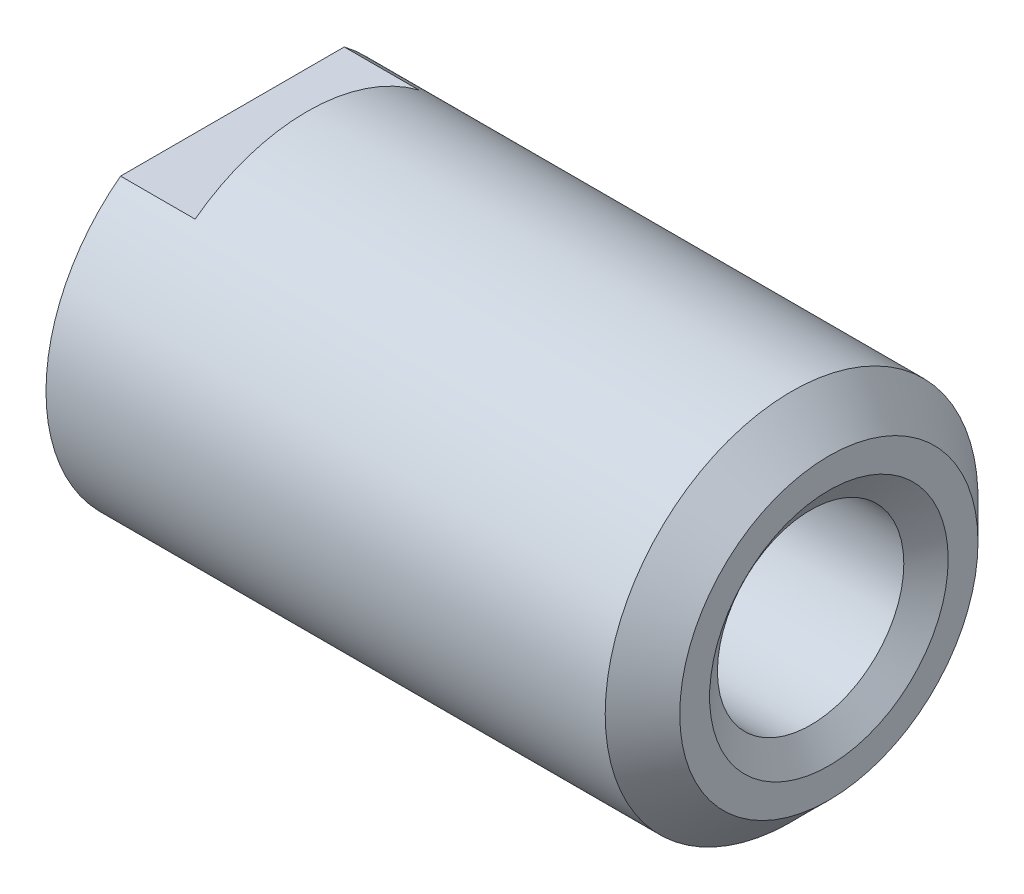
SolidWorks part; units mm, degrees
ref_plane "Спереди" through (0, 0, 0) normal (0, 0, 1) x (1, 0, 0)
ref_plane "Сверху" through (0, 0, 0) normal (0, 1, 0) x (1, 0, 0)
ref_plane "Справа" through (0, 0, 0) normal (1, 0, 0) x (0, 0, -1)
sketch "Эскиз1" plane through (0, 0, 0) normal (0, 0, 1) x (1, 0, 0)
  line L0 (0, 0) -> (16.4018, 0) construction
  line L1 (0, 1.25) -> (0, 2.5)
  line L2 (0, 2.5) -> (8, 2.5)
  line L3 (8, 2.5) -> (8, 1.25)
  line L4 (8, 1.25) -> (0, 1.25)
  dimension "D1" = 2.5
  dimension "D2" = 5
  dimension "D3" = 8
revolve "Повернуть1" add sketch "Эскиз1" angle 360 about L0
cosmetic thread "Отверстие резьбы1" parameters "D2"=3
cosmetic thread "Условное изображение резьбы1" parameters "D1"=5, "D2"=4.11
hole_wizard "Отверстие обработанное метчиком M31" positions "Эскиз3" profile "Эскиз2" tap size "M3" standard "DIN" end condition through all
sketch "Эскиз3" plane through (8, 0, 0) normal (1, 0, 0) x (0, 0, -1)
  circle A0 centre (0, 0) radius 1.25 construction
  point P0 (0, 0)
sketch "Эскиз2" plane through (8, 0, 0) normal (0, 1, 0) x (0, 0, -1)
  line L0 (0, 0) -> (0, 8)
  line L1 (0, 8) -> (1.6, 8)
  line L2 (1.25, 7.7549) -> (1.25, 0.2451)
  line L3 (1.25, 0.2451) -> (1.6, 0)
  line L5 (1.6, 0) -> (0, 0)
  line L6 (-1.25, 0.2451) -> (-1.6, 0) construction
  line L7 (1.6, 8) -> (1.25, 7.7549)
  line L8 (-1.6, 8) -> (-1.25, 7.7549) construction
  line L11 (0, -6.35) -> (0, 107.95) construction
  dimension "Диаметр проходного сверла" = 2.5
  dimension "Глубина проходного сверла" = 8
  dimension "Диаметр передней зенковки" = 3.2
  dimension "Угол передней зенковки" = 110
  dimension "Диаметр задней зенковки" = 3.2
  dimension "Угол задней зенковки" = 110
chamfer "Фаска1" distance 0.5 angle 45 1 edges at (8, 0, 2.5)
sketch "Эскиз4" plane through (0, 0, 0) normal (-1, 0, 0) x (0, 0, 1)
  line L0 (-1.5, 2) -> (1.5, 2)
  line L1 (1.5, -2) -> (-1.5, -2)
  circle A0 centre (0, 0) radius 2.5 construction
  circle M2 centre (0, 0) radius 2.5
  dimension "D1" = 4
extrude "Вырез-Вытянуть1" cut sketch "Эскиз4" against normal blind 1 contours L0 M2 | L1 M2
